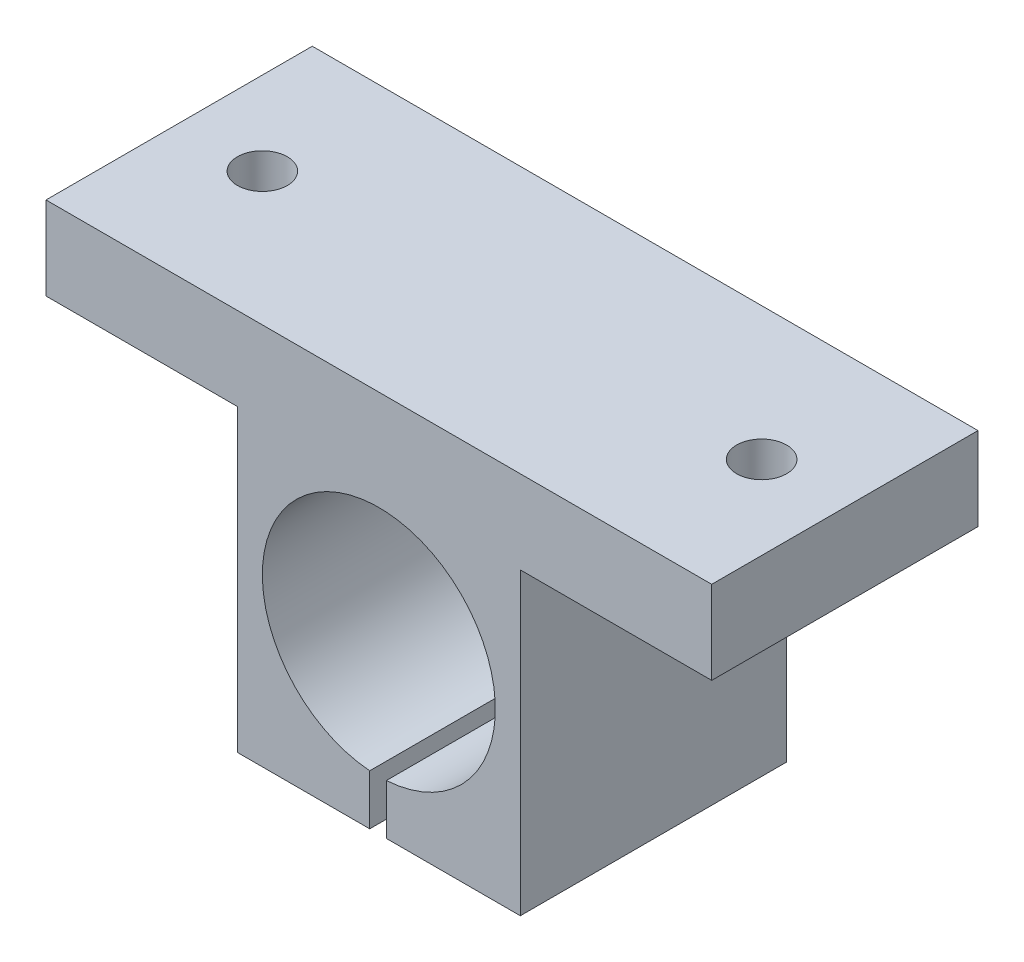
SolidWorks part; units mm, degrees
material "Plástico personalizado"
ref_plane "Plano frontal" through (0, 0, 0) normal (0, 0, 1) x (1, 0, 0)
ref_plane "Plano superior" through (0, 0, 0) normal (0, 1, 0) x (1, 0, 0)
ref_plane "Plano direito" through (0, 0, 0) normal (1, 0, 0) x (0, 0, -1)
sketch "Esboço1" plane through (0, 0, 0) normal (0, 0, 1) x (1, 0, 0)
  line L0 (-20, 8) -> (-8.5, 8)
  line L1 (-8.5, -10) -> (8.5, -10)
  line L2 (-8.5, -10) -> (-8.5, 8)
  line L4 (8.5, -10) -> (8.5, 8)
  line L5 (8.5, 8) -> (20, 8)
  line L8 (-20, 8) -> (-20, 13)
  line L9 (-20, 13) -> (20, 13)
  line L10 (20, 8) -> (20, 13)
  circle A0 centre (0, 0) radius 7
  point P0 (0, 0)
  point P6 (0, 9)
  dimension "D4" = 14
  dimension "D1" = 17
  dimension "D2" = 40
  dimension "D3" = 18
  dimension "D5" = 10
extrude "Ressalto-extrusão1" add sketch "Esboço1" along normal blind 16
sketch "Esboço2" plane through (0, 0, 16) normal (0, 0, 1) x (1, 0, 0)
  line L1 (-0.5487, -11.868) -> (0.4513, -11.868)
  line L2 (-0.5487, -11.868) -> (-0.5487, -6.2203)
  line L3 (-0.5487, -6.2203) -> (0.4513, -6.2203)
  line L4 (0.4513, -11.868) -> (0.4513, -6.2203)
  line L5 (-0.5487, -11.868) -> (0.4513, -6.2203) construction
  line L6 (-0.5487, -6.2203) -> (0.4513, -11.868) construction
  point P0 (-0.0487, -9.0442)
  dimension "D1" = 1
extrude "Corte-extrusão1" cut sketch "Esboço2" against normal through all
sketch "Esboço3" plane through (0, 8, 0) normal (0, -1, 0) x (1, 0, 0)
  line L0 (-20, 16) -> (-20, 0) construction
  line L3 (-20, 0) -> (-8.5, 0) construction
  circle A0 centre (-15, 8) radius 1.5
  dimension "D2" = 3
  dimension "D1" = 5
  dimension "D3" = 8
extrude "Corte-extrusão2" cut sketch "Esboço3" against normal blind 16
mirror "Espelhar1" about plane through (0, 0, 0) normal (1, 0, 0) of "Corte-extrusão2"
